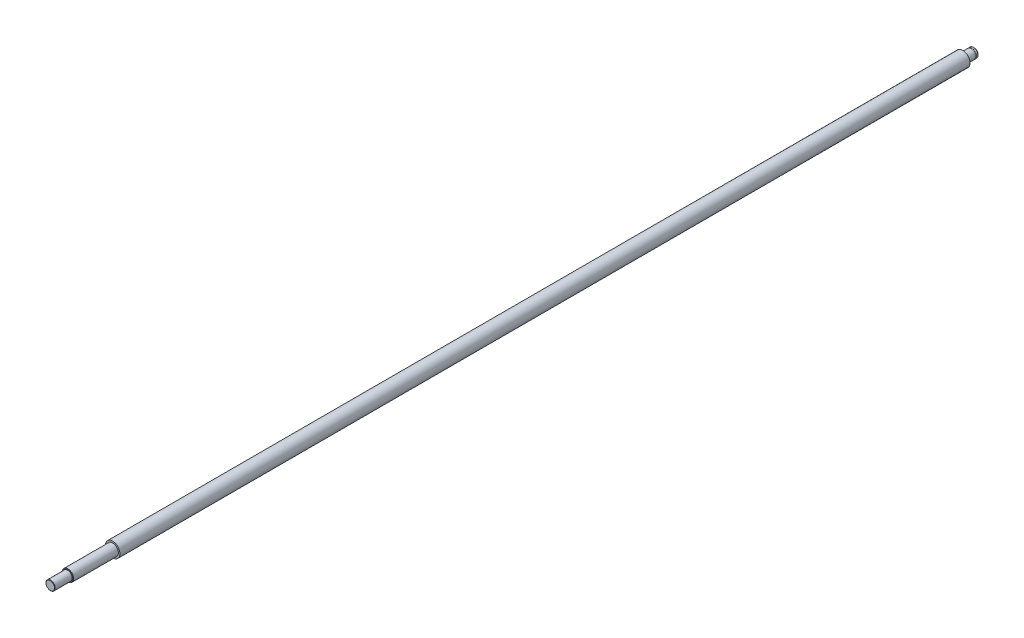
SolidWorks part; units mm, degrees
material "Plain Carbon Steel"
ref_plane "Front Plane" through (0, 0, 0) normal (0, 0, 1) x (1, 0, 0)
ref_plane "Top Plane" through (0, 0, 0) normal (0, 1, 0) x (1, 0, 0)
ref_plane "Right Plane" through (0, 0, 0) normal (1, 0, 0) x (0, 0, -1)
sketch "Sketch1" plane through (0, 0, 0) normal (1, 0, 0) x (0, 0, -1)
  line L0 (-400, 0) -> (400, 0)
  line L1 (-400, 0) -> (-400, 4)
  line L2 (-400, 4) -> (-385, 4)
  line L3 (-385, 4) -> (-385, 4.94)
  line L4 (-385, 4.94) -> (-346, 4.94)
  line L5 (-346, 4.94) -> (-346, 6.32)
  line L6 (-346, 6.32) -> (390, 6.32)
  line L7 (390, 6.32) -> (390, 4)
  line L8 (390, 4) -> (400, 4)
  line L9 (400, 4) -> (400, 0)
  dimension "D1" = 800
  dimension "D2" = 15
  dimension "D3" = 39
  dimension "D4" = 10
  dimension "D5" = 4
  dimension "D6" = 6.32
  dimension "D7" = 4.94
  dimension "D8" = 4
revolve "Revolve1" add sketch "Sketch1" angle 360 about L0
cosmetic thread "Cosmetic Thread1" parameters "D2"=6.619
sketch "Sketch2" plane through (0, 0, 0) normal (1, 0, 0) x (0, 0, -1)
  line L0 (400, 4) -> (390, 4) construction
  line L1 (397.9, 4) -> (397, 4)
  line L2 (397.9, 4) -> (397.9, 3.8)
  line L3 (397.9, 3.8) -> (397, 3.8)
  line L4 (397, 4) -> (397, 3.8)
  line L5 (400, -4) -> (400, 4) construction
  line L6 (400, 0) -> (390, 0) construction
  line L7 (390, -6.32) -> (390, 6.32) construction
  dimension "D1" = 0.9
  dimension "D2" = 2.1
  dimension "D3" = 3.8
revolve "Cut-Revolve1" cut sketch "Sketch2" angle 360 about L6
chamfer "Chamfer1" distance 0.8 angle 45 1 edges at (4, 0, -400)
chamfer "Chamfer2" distance 0.3 angle 45 2 edges at (4, 0, 400) (4.94, 0, 385)
equation "\"length\"= 800mm"
equation "\"D1@Sketch1\" = \"work_area_depth\"-100"
equation "\"M5_tap\"=4.2mm\t\t\t\t\t\t\t' Below you can do mesurements as follows: cm, mm, ft, in, m, "
equation "\"M5_clearence\"=5.5mm"
equation "\"M6_tap\"=5mm"
equation "\"M6_clearence\"=6.6mm"
equation "\"work_area_width\"=1100mm"
equation "\"work_area_depth\"=900mm"
